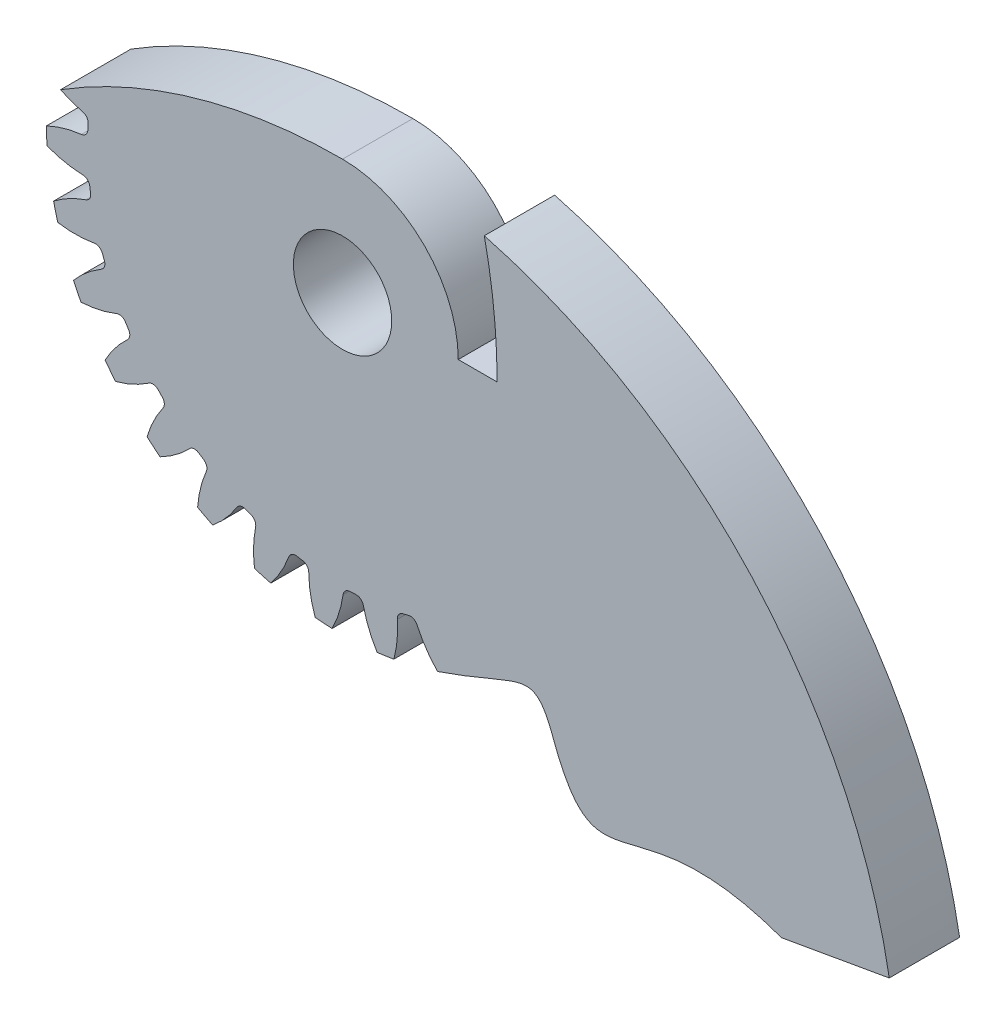
SolidWorks part; units mm, degrees
material "ABS"
ref_plane "Front" through (0, 0, 0) normal (0, 0, 1) x (1, 0, 0)
ref_plane "Top" through (0, 0, 0) normal (0, 1, 0) x (1, 0, 0)
ref_plane "Right" through (0, 0, 0) normal (1, 0, 0) x (0, 0, -1)
sketch "Sketch3" plane through (0, 0, 0) normal (0, 0, 1) x (1, 0, 0)
  circle A0 centre (0, 0) radius 40.64
  dimension "od" = 81.28
extrude "gearBody" add sketch "Sketch3" along normal blind 9.652
sketch "Sketch2" plane through (0, 0, 0) normal (0, 0, 1) x (1, 0, 0)
  line L0 (0, 0) -> (34.0786, 14.1158) construction
  line L1 (45.4751, -11.4855) -> (0, 0) construction
  line L2 (0, 0) -> (36.3143, 0) construction
  line L3 (38.0972, -0.458) -> (37.8451, -4.4001) construction
  line L5 (37.9712, -2.4291) -> (0, 0) construction
  line L7 (0, 0) -> (36.8864, 0) construction
  arc A0 (36.879, -0.7403) -> (36.6727, -3.9649) centre (0, 0) ccw construction
  arc A1 (40.637, 0.4947) -> (40.2427, -5.6687) centre (0, 0) ccw construction
  arc A2 (38.0972, -0.458) -> (37.8451, -4.4001) centre (0, 0) ccw construction
  arc A3 (34.9015, -2.6404) -> (34.9534, -1.8283) centre (0, 0) ccw
  arc A4 (45.4751, -11.4855) -> (35.6466, -3.6712) centre (32.0022, -18.3431) ccw
  arc A5 (45.4751, -11.4855) -> (46.5679, 5.5974) centre (0, 0) ccw
  arc A6 (46.5679, 5.5974) -> (35.8238, -0.9008) centre (34.0786, 14.1158) cw
  arc A7 (34.9534, -1.8283) -> (35.8238, -0.9008) centre (35.9376, -1.8798) cw
  arc A8 (35.6466, -3.6712) -> (34.9015, -2.6404) centre (35.8842, -2.7147) cw
  point P6 (46.5679, 5.5974)
  point P22 (45.4751, -11.4855)
  dimension "baseDia" = 73.7729
  dimension "od" = 81.28
  dimension "pd" = 76.2
  dimension "rd" = 70.0024
  dimension "rFillet" = 0.9855
  dimension "pointX" = 46.5679
  dimension "pointY" = 5.5974
  dimension "CTT" = 3.9421
  dimension "flankCenterAngle" = 22.5
extrude "toothCut" cut sketch "Sketch2" along normal through all
pattern_circular "CirPattern1" count 30 over 360 about axis through (0, 0, 0) along (0, 0, 1) of "toothCut"
sketch "hub1Dia" plane through (0, 0, 0) normal (0, 0, -1) x (-1, 0, 0)
  circle A0 centre (0, 0) radius 12.7
  dimension "hub1Dia" = 25.4
sketch "hub2Dia" plane through (0, 0, 9.652) normal (0, 0, 1) x (1, 0, 0)
  circle A0 centre (0, 0) radius 12.7
  dimension "hub2dia" = 25.4
sketch "boreDia" plane through (0, 0, 0) normal (0, 0, 1) x (1, 0, 0)
  circle A0 centre (0, 0) radius 6.7469
  dimension "boreDia" = 13.4937
extrude "bore" cut sketch "boreDia" against normal mid plane 25400
sketch "Sketch4" plane through (0, 0, 9.652) normal (0, 0, 1) x (1, 0, 0)
  circle A0 centre (0, -57.15) radius 76.1746
  arc A2 (-41.7195, 6.5842) -> (41.7195, 6.5842) centre (0, 0) cw
  dimension "D1" = 152.3492
  dimension "D2" = 57.15
extrude "Cut-Extrude1" cut sketch "Sketch4" against normal through all
sketch "Sketch5" plane through (0, 0, 9.652) normal (0, 0, 1) x (1, 0, 0)
  line L0 (0, 19.0246) -> (21.5163, 3.7176)
  line L1 (21.5163, 3.7176) -> (8.9608, -26.928)
  line L2 (8.9608, -26.928) -> (13.028, -38.4952)
  line L3 (0, 0) -> (0, -57.15) construction
  line L4 (0, -57.15) -> (-54.1615, -3.586) construction
  line L5 (0, -57.15) -> (65.9691, -95.2373) construction
  line L9 (0, -57.15) -> (75.0173, -43.9224) construction
  line L12 (60.232, -46.5295) -> (75.0173, -43.9224)
  line L13 (0, -57.15) -> (29.696, -40.005) construction
  line L14 (29.696, -40.005) -> (26.521, -34.5057) construction
  circle A1 centre (0, -57.15) radius 76.1746 construction
  arc A5 (0, 19.0246) -> (75.0173, -43.9224) centre (0, -57.15) cw
  circle A6 centre (0, -57.15) radius 21.59 construction
  circle A12 centre (49.4934, -85.725) radius 40.64 construction
  spline S0 degree 3 poles (13.028, -38.4952) (20.557, -35.948) (26.6517, -31.726) (34.6651, -56.7545) (39.5345, -39.0169) (60.232, -46.5295) knots 0 0 0 0 0.118515 0.218515 1 1 1 1
  point P28 (21.569, -56.1981)
  dimension "D1" = 43.18
  dimension "D3" = 81.28
  dimension "D6" = 152.3492
  dimension "D2" = 120
  dimension "D4" = 57.15
  dimension "D8" = 57.15
  dimension "D7" = 60
  dimension "D9" = 34.29
  dimension "D10" = 6.35
  dimension "D5" = 80
extrude "Boss-Extrude1" add sketch "Sketch5" against normal up to surface (9.652 mm away) up to face at (6.7469, 0, 0)
sketch "Sketch6" plane through (0, 0, 9.652) normal (0, 0, 1) x (1, 0, 0)
  line L1 (-41.2993, 3.0747) -> (-42.3397, 6.1739)
  line L2 (15.875, 0) -> (21.209, 0)
  circle A0 centre (0, -57.15) radius 76.1746 construction
  arc A1 (75.0173, -43.9224) -> (-34.0662, 10.9827) centre (0, -57.15) ccw construction
  circle A2 centre (0, 0) radius 15.875 construction
  arc A3 (0, 15.875) -> (15.875, 0) centre (0, 0) cw
  arc A4 (19.4523, 16.499) -> (-42.3397, 6.1739) centre (0, -57.15) ccw
  arc A5 (0, 15.875) -> (-41.2993, 3.0747) centre (0, -57.15) ccw
  circle A6 centre (0, 0) radius 21.209 construction
  circle A8 centre (-57.15, 0) radius 78.359 construction
  arc A9 (21.209, 0) -> (19.4523, 16.499) centre (-57.15, 0) ccw
  dimension "D4" = 57.15
  dimension "D1" = 31.75
  dimension "D2" = 42.418
  dimension "D3" = 156.718
extrude "Cut-Extrude2" cut sketch "Sketch6" against normal through all
equation "\"Bodytube_OD\" = 6.17in"
equation "\"Bodytube_ID\" = 5.998in"
equation "\"Fwd_Tube_Length\" = 40in"
equation "\"Mid_Tube_Length\" = 1in"
equation "\"Aft_Section_Length\"= 39in"
equation "\"Mid_Coupler_Length\"= 13in"
equation "\"Aft_Lower_Length\"= 22in"
equation "\"AB_Coupler_OD_Length\"= 1in"
equation "\"AB_Coupling_Section_Length\"= 0.375in"
equation "\"AB_Coupler_Length\"= \"AB_Coupler_OD_Length\" + \"AB_Coupling_Section_Length\" * 2"
equation "\"Cutout_Angle\" = 80"
equation "\"AB_Paddle_Height\" = 0.375in"
equation "\"AB_Coupler_Num_Screws\"= 6"
equation "\"Num_Cutouts\" = 3"
equation "\"AB_Coupler_OD\"= 6.17in"
equation "\"AB_Coupler_ID\"= 5.75in"
equation "\"AB_Coupler_Surface_Diameter\"= 5.998in"
equation "\"AB_Coupling_Screw_Diameter\"= 0.1065in"
equation "\"AB_Central_Bushing_Length\" = .75in"
equation "\"Lead_Screw_Dist\" = 3.4in"
equation "\"Lead_Screw_Diam\" = 0.386in"
equation "\"Lead_Screw_Length\" = (\"Mid_Coupler_Length\" + 2*0.375in + 2*0.5in)"
equation "\"Paddle_Pin_Offset\" = .25in"
equation "\"Paddle_Pin_Radius\" = 2.25in"
equation "\"Fwd_BKHD_From_Top\" = 18in"
equation "\"D1@Sketch4\"=\"Bodytube_ID\""
equation "\"D2@Sketch4\"=\"Paddle_Pin_Radius\""
equation "\"D3@Sketch5\"=\"Paddle_Gear_OD\""
equation "\"D4@Sketch5\"=\"Paddle_Pin_Radius\""
equation "\"Motor_OD\" = 4in"
equation "\"Aft_Upper_Length\"= \"Aft_Section_Length\" - \"Aft_Lower_Length\" - \"AB_Coupler_OD_Length\""
equation "\"Paddle_Gear_OD\" = 3.2in"
equation "\"D5@Sketch5\"=\"Cutout_Angle\""
equation "\"D6@Sketch5\"=\"Bodytube_ID\""
equation "\"D1@Sketch6\"=\"AB_Coupler_ID\"-2*\"Paddle_Pin_Radius\""
equation "\"D2@Sketch6\"=\"Bodytube_OD\"-2*\"Paddle_Pin_Radius\""
equation "\"D3@Sketch6\"=\"Bodytube_OD\""
equation "\"D4@Sketch6\"=\"Paddle_Pin_Radius\""
equation "\"D8@Sketch5\"=\"Paddle_Pin_Radius\""
equation "\"Drive_Gear_OD\" = 1.7in"
equation "\"Fin_Thickness\"= .118in"
equation "\"Guiderail_Cutout_Diameter\"= 1.5in"
equation "\"DB9_Hole_Dist\" = 25mm"
equation "\"D1@Sketch5\"=\"Drive_Gear_OD\""
